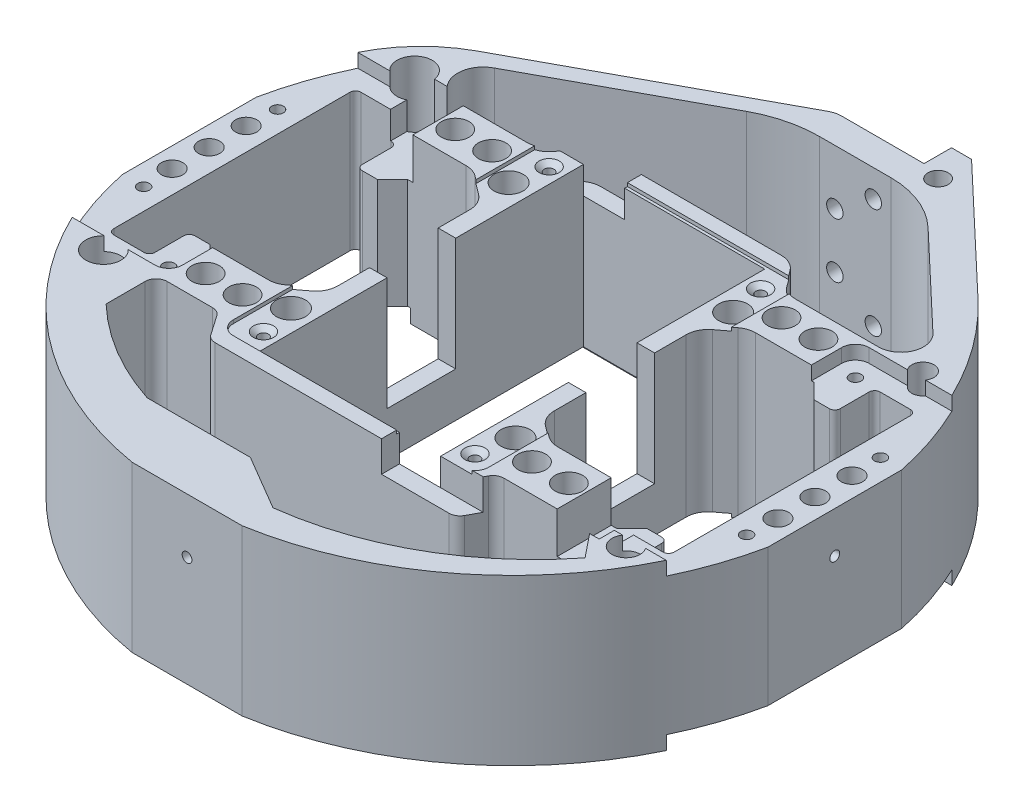
SolidWorks part; units mm, degrees
material "6061 Alloy"
ref_plane "Front Plane" through (0, 0, 0) normal (0, 0, 1) x (1, 0, 0)
ref_plane "Top Plane" through (0, 0, 0) normal (0, 1, 0) x (1, 0, 0)
ref_plane "Right Plane" through (0, 0, 0) normal (1, 0, 0) x (0, 0, -1)
sketch "Sketch1" plane through (0, 0, 0) normal (0, 1, 0) x (1, 0, 0)
  line L0 (-1000, 0) -> (49000, 0) construction
  line L1 (0, -1000) -> (0, 49000) construction
  line L2 (20.955, 37.465) -> (-20.955, 37.465)
  line L3 (-20.955, 37.465) -> (-20.955, 0)
  line L4 (-53.975, 19.3675) -> (-50.4825, 19.3675)
  line L5 (-50.4825, 19.3675) -> (-46.99, 22.86)
  line L6 (-46.99, 22.86) -> (-33.4518, 22.86)
  line L7 (-30.3916, 21.8348) -> (-27.0388, 19.3044)
  line L8 (-74.6125, 15.473) -> (-74.6125, -15.473)
  line L9 (-25.019, 15.2496) -> (-25.019, 0)
  line L10 (74.6125, 15.473) -> (74.6125, -15.473)
  line L11 (0, 76.2) -> (4.1152, 76.2) construction
  line L12 (-55.245, 20.6375) -> (-55.245, 27.305)
  line L13 (-56.515, 28.575) -> (-63.5, 28.575)
  line L14 (-64.77, 27.305) -> (-64.77, -27.305)
  line L15 (64.77, 27.305) -> (64.77, -27.305)
  line L16 (56.515, 28.575) -> (63.5, 28.575)
  line L17 (55.245, 20.6375) -> (55.245, 27.305)
  line L19 (0, 76.2) -> (19.05, 76.2)
  line L20 (25.019, 15.2496) -> (25.019, 0)
  line L21 (-20.846, 41.3381) -> (0, 41.3381)
  line L22 (30.3916, 21.8348) -> (27.0388, 19.3044)
  line L23 (46.99, 22.86) -> (33.4518, 22.86)
  line L24 (46.99, 22.86) -> (50.4825, 19.3675)
  line L25 (53.975, 19.3675) -> (50.4825, 19.3675)
  line L26 (20.955, 37.465) -> (20.955, 0)
  line L27 (20.955, -37.465) -> (20.955, 0)
  line L28 (53.975, -19.3675) -> (50.4825, -19.3675)
  line L29 (46.99, -22.86) -> (50.4825, -19.3675)
  line L30 (46.99, -22.86) -> (33.4518, -22.86)
  line L31 (30.3916, -21.8348) -> (27.0388, -19.3044)
  line L32 (24.9874, 39.2758) -> (27.197, 36.2837)
  line L33 (25.019, -15.2496) -> (25.019, 0)
  line L34 (19.05, 76.2) -> (19.05, 82.55)
  line L35 (19.05, 82.55) -> (23.6855, 82.55)
  line L36 (55.245, -20.6375) -> (55.245, -27.305)
  line L37 (56.515, -28.575) -> (63.5, -28.575)
  line L38 (-56.515, -28.575) -> (-63.5, -28.575)
  line L39 (-55.245, -20.6375) -> (-55.245, -27.305)
  line L40 (-23.8543, -60.4955) -> (0, -60.4955)
  line L41 (52.4298, 55.2951) -> (23.6855, 82.55)
  line L42 (-25.019, -15.2496) -> (-25.019, 0)
  line L43 (31.2835, 34.2214) -> (50.4563, 34.2214)
  line L44 (-30.3916, -21.8348) -> (-27.0388, -19.3044)
  line L45 (-46.99, -22.86) -> (-33.4518, -22.86)
  line L46 (-50.4825, -19.3675) -> (-46.99, -22.86)
  line L47 (-53.975, -19.3675) -> (-50.4825, -19.3675)
  line L48 (-20.955, -37.465) -> (-20.955, 0)
  line L49 (20.955, -37.465) -> (-20.955, -37.465)
  line L50 (-44.8593, -34.8822) -> (-34.3568, -34.8822)
  line L51 (-47.0915, 34.5231) -> (-31.087, 34.5231)
  line L52 (-27.0577, 36.5094) -> (-24.8753, 39.3518)
  line L53 (0, 41.3381) -> (20.9009, 41.3381)
  line L54 (54.0568, 43.2516) -> (32.3487, 63.8349)
  line L55 (18.015, 69.55) -> (1.5516, 69.55)
  line L56 (-32.2697, -35.9746) -> (-29.1259, -40.5071)
  line L57 (-27.0388, -41.5995) -> (27.0388, -41.5995)
  line L58 (-47.3993, -37.4222) -> (-47.3993, -46.4548)
  line L59 (54.276, -36.2937) -> (58.8069, -41.9283)
  line L60 (31.2258, -36.6729) -> (29.2707, -40.272)
  line L61 (52.2966, -35.3453) -> (33.4578, -35.3453)
  line L62 (-11.9532, 66.1301) -> (-49.7073, 45.6984)
  line L63 (-55.1504, 47.0849) -> (-2.539, 75.557)
  line L64 (0, -60.4955) -> (12.7, -67.9689)
  line L65 (12.7, -75.1342) -> (-12.7, -75.1342)
  arc A0 (-55.1504, 47.0849) -> (-68.875, 32.5987) centre (-39.8854, 18.8779) ccw
  arc A1 (63.5, -28.575) -> (64.77, -27.305) centre (63.5, -27.305) ccw
  arc A2 (64.77, 27.305) -> (63.5, 28.575) centre (63.5, 27.305) ccw
  arc A3 (-63.5, -28.575) -> (-64.77, -27.305) centre (-63.5, -27.305) cw
  arc A4 (-63.5, 28.575) -> (-64.77, 27.305) centre (-63.5, 27.305) ccw
  arc A5 (74.6125, 15.473) -> (52.4298, 55.2951) centre (0, 0) ccw
  arc A6 (-74.6125, -15.473) -> (-12.7, -75.1342) centre (0, 0) ccw
  arc A7 (55.245, -27.305) -> (56.515, -28.575) centre (56.515, -27.305) ccw
  arc A8 (56.515, 28.575) -> (55.245, 27.305) centre (56.515, 27.305) ccw
  arc A9 (-56.515, -28.575) -> (-55.245, -27.305) centre (-56.515, -27.305) ccw
  arc A10 (-55.245, 27.305) -> (-56.515, 28.575) centre (-56.515, 27.305) ccw
  arc A15 (50.4563, 34.2214) -> (54.0568, 43.2516) centre (50.4563, 39.4543) ccw
  arc A16 (-49.7073, 45.6984) -> (-47.0915, 34.5231) centre (-47.0915, 40.4169) ccw
  arc A17 (32.3487, 63.8349) -> (18.015, 69.55) centre (18.015, 48.7178) ccw
  arc A18 (-68.875, 32.5987) -> (-74.6125, 15.473) centre (0, 0) ccw
  arc A19 (12.7, -67.9689) -> (58.8069, -41.9283) centre (4.0432, 1.1967) ccw
  arc A20 (-47.3993, -46.4548) -> (-23.8543, -60.4955) centre (-4.9282, -1.9967) ccw
  arc A21 (12.7, -75.1342) -> (74.6125, -15.473) centre (0, 0) ccw
  circle A22 centre (23.6855, 74.8125) radius 2.3565
  circle A23 centre (-25.954, 25.1591) radius 3.3565
  arc A24 (-30.3916, -21.8348) -> (-33.4518, -22.86) centre (-33.4518, -17.78) cw
  arc A25 (-33.4518, 22.86) -> (-30.3916, 21.8348) centre (-33.4518, 17.78) cw
  arc A26 (30.3916, 21.8348) -> (33.4518, 22.86) centre (33.4518, 17.78) cw
  arc A27 (33.4518, -22.86) -> (30.3916, -21.8348) centre (33.4518, -17.78) cw
  arc A28 (27.0388, -19.3044) -> (25.019, -15.2496) centre (30.099, -15.2496) cw
  arc A29 (25.019, 15.2496) -> (27.0388, 19.3044) centre (30.099, 15.2496) cw
  arc A30 (-25.019, -15.2496) -> (-27.0388, -19.3044) centre (-30.099, -15.2496) cw
  arc A31 (-27.0388, 19.3044) -> (-25.019, 15.2496) centre (-30.099, 15.2496) cw
  arc A32 (53.975, -19.3675) -> (55.245, -20.6375) centre (53.975, -20.6375) cw
  arc A34 (55.245, 20.6375) -> (53.975, 19.3675) centre (53.975, 20.6375) cw
  arc A37 (-55.245, -20.6375) -> (-53.975, -19.3675) centre (-53.975, -20.6375) cw
  arc A38 (-53.975, 19.3675) -> (-55.245, 20.6375) centre (-53.975, 20.6375) cw
  circle A40 centre (-41.9877, 28.8501) radius 3.175
  circle A41 centre (41.9877, 28.8501) radius 3.175
  circle A42 centre (-41.9877, -28.8501) radius 3.175
  circle A43 centre (41.9877, -28.8501) radius 3.175
  circle A44 centre (-33.4518, 28.8501) radius 3.175
  circle A45 centre (33.4518, 28.8501) radius 3.175
  circle A46 centre (-33.4518, -28.8501) radius 3.175
  circle A47 centre (33.4518, -28.8501) radius 3.175
  circle A48 centre (-58.4996, 35.9746) radius 4.0647
  circle A49 centre (60.46, 34.5231) radius 2.5554
  circle A50 centre (-58.4996, -35.9746) radius 4.0647
  circle A51 centre (61.2367, -34.8822) radius 3.2423
  circle A52 centre (25.954, 25.1591) radius 3.3565
  circle A53 centre (25.954, -25.1591) radius 3.3565
  circle A54 centre (-25.954, -25.1591) radius 3.3565
  arc A55 (-27.0388, -41.5995) -> (-29.1259, -40.5071) centre (-27.0388, -39.0595) cw
  arc A56 (-34.3568, -34.8822) -> (-32.2697, -35.9746) centre (-34.3568, -37.4222) cw
  circle A57 centre (70.0256, 8.5625) radius 2.4628
  circle A58 centre (-70.0256, 8.5625) radius 2.4628
  circle A59 centre (70.0256, -8.5625) radius 2.4628
  circle A60 centre (-70.0256, -8.5625) radius 2.4628
  arc A61 (54.276, -36.2937) -> (52.2966, -35.3453) centre (52.2966, -37.8853) ccw
  arc A62 (31.2258, -36.6729) -> (33.4578, -35.3453) centre (33.4578, -37.8853) cw
  arc A63 (29.2707, -40.272) -> (27.0388, -41.5995) centre (27.0388, -39.0595) cw
  arc A64 (-44.8593, -34.8822) -> (-47.3993, -37.4222) centre (-44.8593, -37.4222) ccw
  circle A69 centre (-70.0256, 0) radius 2.4628
  circle A70 centre (70.0256, 0) radius 2.4628
  arc A71 (27.197, 36.2837) -> (31.2835, 34.2214) centre (31.2835, 39.3014) ccw
  arc A72 (20.9009, 41.3381) -> (24.9874, 39.2758) centre (20.9009, 36.2581) cw
  arc A73 (-31.087, 34.5231) -> (-27.0577, 36.5094) centre (-31.087, 39.6031) ccw
  arc A74 (-24.8753, 39.3518) -> (-20.846, 41.3381) centre (-20.846, 36.2581) cw
  arc A75 (-11.9532, 66.1301) -> (1.5516, 69.55) centre (1.5516, 41.1755) cw
  arc A76 (-2.539, 75.557) -> (0, 76.2) centre (0, 70.8654) cw
  point P34 (0, 37.465)
  point P44 (64.77, -28.575)
  point P49 (64.77, 0)
  point P50 (-64.77, 0)
  point P52 (55.245, -28.575)
  point P62 (64.77, 28.575)
  point P65 (-64.77, -28.575)
  point P68 (-64.77, 28.575)
  point P70 (-74.6125, 0)
  point P96 (-31.75, -22.86)
  point P99 (55.245, 28.575)
  point P103 (-55.245, -28.575)
  point P106 (-55.245, 28.575)
  point P111 (-48.26, -22.86)
  point P114 (48.26, -22.86)
  point P117 (48.26, 22.86)
  point P120 (-48.26, 22.86)
  point P124 (-31.75, 22.86)
  point P127 (31.75, 22.86)
  point P130 (31.75, -22.86)
  point P133 (25.019, -17.78)
  point P136 (25.019, 17.78)
  point P139 (-25.019, -17.78)
  point P142 (-25.019, 17.78)
  point P145 (55.245, -19.3675)
  point P148 (48.26, -19.3675)
  point P151 (55.245, 19.3675)
  point P154 (48.26, 19.3675)
  point P157 (-48.26, -19.3675)
  point P160 (-55.245, -19.3675)
  point P163 (-55.245, 19.3675)
  point P166 (-48.26, 19.3675)
  point P195 (0, -41.5995)
  point P218 (53.5134, -35.3453)
  point P221 (31.947, -35.3453)
  point P224 (28.5496, -41.5995)
  point P258 (-5.6338, 69.55)
  dimension "D2" = 41.91
  dimension "D7" = 1.27
  dimension "D10" = 1.27
  dimension "D16" = 21.971
  dimension "D3" = 5.08
  dimension "D22" = 1.27
  dimension "D23" = 2.54
  dimension "D14" = 6.35
  dimension "D24" = 38.735
  dimension "D25" = 5.08
  dimension "D26" = 4.6355
  dimension "D27" = 21.971
  dimension "D19" = 2.54
  dimension "D33" = 45
  dimension "D4" = 16.51
  dimension "D5" = 45.72
  dimension "D6" = 74.93
  dimension "D8" = 149.225
  dimension "D9" = 9.525
  dimension "D11" = 45
  dimension "D12" = 4.064
  dimension "D13" = 57.15
  dimension "D15" = 35.56
  dimension "D18" = 19.05
  dimension "D20" = 7.62
  dimension "D21" = 25.4
  dimension "D28" = 76.2
  dimension "D29" = 3.81
  dimension "D31" = 45
  dimension "D32" = 21.971
  dimension "D34" = 21.971
  dimension "D35" = 45
extrude "Boss-Extrude1" add sketch "Sketch1" along normal blind 38.1
ref_plane "Plane1" through (0, 19.05, 0) normal (0, 1, 0) x (-1, 0, 0)
ref_plane "Plane2" through (0, 0, 0) normal (-1, 0, 0) x (0, 0, 1)
sketch "Sketch2" plane through (0, 38.1, 0) normal (0, 1, 0) x (1, 0, 0)
  line L0 (-25.019, -15.2496) -> (-25.019, 15.2496) construction
  line L1 (-25.019, 7.9375) -> (-20.955, 7.9375)
  line L2 (-25.019, 7.9375) -> (-25.019, -7.9375)
  line L3 (-25.019, -7.9375) -> (-20.955, -7.9375)
  line L4 (-20.955, 7.9375) -> (-20.955, -7.9375)
  line L5 (-20.955, 37.465) -> (-20.955, -37.465) construction
  line L6 (20.955, -37.465) -> (20.955, 37.465) construction
  line L7 (20.955, 7.9375) -> (25.019, 7.9375)
  line L8 (20.955, 7.9375) -> (20.955, -7.9375)
  line L9 (20.955, -7.9375) -> (25.019, -7.9375)
  line L10 (25.019, 7.9375) -> (25.019, -7.9375)
  line L11 (25.019, 15.2496) -> (25.019, -15.2496) construction
  line L12 (25.019, 0) -> (-25.019, 0) construction
  dimension "D1" = 15.875
extrude "Cut-Extrude1" cut sketch "Sketch2" against normal blind 26.9875
sketch "Sketch3" plane through (0, 38.1, 0) normal (0, 1, 0) x (1, 0, 0)
  line L1 (-49.53, 33.02) -> (-80.0114, 33.02)
  line L2 (-46.355, 29.845) -> (-46.355, -29.845)
  line L3 (-49.53, -33.02) -> (-80.0114, -33.02)
  line L4 (-80.0114, 33.02) -> (-80.0114, -33.02)
  line L6 (-55.245, 20.6375) -> (-55.245, 27.305) construction
  line L7 (0, -1000) -> (0, 49000) construction
  line L8 (80.0114, 33.02) -> (80.0114, -33.02)
  line L9 (49.53, -33.02) -> (80.0114, -33.02)
  line L10 (46.355, 29.845) -> (46.355, -29.845)
  line L11 (49.53, 33.02) -> (80.0114, 33.02)
  arc A0 (-46.355, -29.845) -> (-49.53, -33.02) centre (-49.53, -29.845) cw
  arc A1 (-49.53, 33.02) -> (-46.355, 29.845) centre (-49.53, 29.845) cw
  arc A2 (49.53, 33.02) -> (46.355, 29.845) centre (49.53, 29.845) ccw
  arc A3 (46.355, -29.845) -> (49.53, -33.02) centre (49.53, -29.845) ccw
  dimension "D2" = 3.175
  dimension "D1" = 8.89
  dimension "D3" = 66.04
  dimension "D4" = 33.02
extrude "Cut-Extrude2" cut sketch "Sketch3" against normal blind 3.175
sketch "Sketch4" plane through (0, 34.925, 0) normal (0, 1, 0) x (1, 0, 0)
  line L2 (-1000, 0) -> (49000, 0) construction
  line L3 (0, -1000) -> (0, 49000) construction
  circle A0 centre (-50.8, 28.575) radius 1.3525
  circle A1 centre (-69.6913, 15.473) radius 1.3525
  circle A2 centre (69.6912, 15.473) radius 1.3526
  circle A3 centre (50.8, 28.575) radius 1.3525
  circle A4 centre (50.8, -28.575) radius 1.3525
  circle A5 centre (69.6912, -15.473) radius 1.3526
  circle A6 centre (-69.6913, -15.473) radius 1.3525
  circle A7 centre (-50.8, -28.575) radius 1.3525
  dimension "D1" = 2.7051
  dimension "D3" = 28.575
  dimension "D4" = 50.8
extrude "Cut-Extrude3" cut sketch "Sketch4" against normal blind 6.35
mirror "Mirror1" about plane through (0, 19.05, 0) normal (0, 1, 0) of "Cut-Extrude3", "Cut-Extrude2"
sketch "Sketch5" plane through (0, 34.925, 0) normal (0, 1, 0) x (1, 0, 0)
  line L1 (-45.7864, 36.5249) -> (-56.6704, 36.5249)
  line L2 (-56.6704, 36.5249) -> (-56.6704, 17.5524)
  line L3 (-56.6704, 17.5524) -> (-45.7864, 17.5524)
  line L4 (-45.7864, 36.5249) -> (-45.7864, 17.5524)
  line L5 (45.7864, -36.5249) -> (56.6704, -36.5249)
  line L6 (56.6704, -36.5249) -> (56.6704, -17.5524)
  line L7 (56.6704, -17.5524) -> (45.7864, -17.5524)
  line L8 (45.7864, -36.5249) -> (45.7864, -17.5524)
  line L10 (-57.3818, 22.86) -> (-41.566, 22.86) [skipped]
  line L11 (57.3818, -22.86) -> (41.566, -22.86) [skipped]
  dimension "D1" = 2
extrude "Cut-Extrude4" cut sketch "Sketch5" against normal mid plane 12.7
sketch "Sketch9" plane through (0, 38.1, 0) normal (0, 1, 0) x (1, 0, 0)
  line L0 (-20.955, 37.465) -> (-20.955, 7.9375) construction
  line L1 (-20.955, 34.3266) -> (-11.43, 34.3266)
  line L2 (-20.955, 34.3266) -> (-20.955, 37.465)
  line L3 (-20.955, 45.3771) -> (-11.43, 45.3771)
  line L4 (-11.43, 34.3266) -> (-11.43, 45.3771)
  line L5 (20.955, -34.3266) -> (11.43, -34.3266)
  line L6 (20.955, -34.3266) -> (20.955, -37.465)
  line L7 (20.955, -45.3771) -> (11.43, -45.3771)
  line L8 (11.43, -34.3266) -> (11.43, -45.3771)
  line L9 (-20.955, 45.3771) -> (-29.4619, 45.3771)
  line L10 (-29.4619, 45.3771) -> (-29.4619, 37.465)
  line L11 (-29.4619, 37.465) -> (-20.955, 37.465)
  line L12 (20.955, -37.465) -> (32.398, -37.465)
  line L13 (32.398, -37.465) -> (32.398, -45.3771)
  line L14 (32.398, -45.3771) -> (20.955, -45.3771)
  dimension "D1" = 9.525
  dimension "D2" = 2
extrude "Cut-Extrude7" cut sketch "Sketch9" against normal blind 7.112
sketch "Sketch10" plane through (0, 0, -76.2) normal (0, 0, -1) x (-1, 0, 0)
  circle A0 centre (-13.97, 31.75) radius 1.8987
  circle A1 centre (-5.08, 25.4) radius 1.8986
  circle A2 centre (-5.08, 12.7) radius 1.8986
  circle A3 centre (-13.97, 6.35) radius 1.8987
  circle A4 centre (-13.97, 31.75) radius 1.8987 construction
  circle A5 centre (-5.08, 25.4) radius 1.8986 construction
  circle A6 centre (-5.08, 12.7) radius 1.8986 construction
  circle A7 centre (-13.97, 6.35) radius 1.8987 construction
extrude "Cut-Extrude8" cut sketch "Sketch10" against normal up to next
sketch "Sketch11" plane through (-74.6125, 0, 0) normal (-1, 0, 0) x (0, 0, 1)
  line L0 (15.473, 34.925) -> (-15.473, 34.925) construction
  circle A0 centre (0, 25.4) radius 1.1303
  point P4 (0, 34.925)
  point P5 (0, 34.925)
  dimension "D1" = 2.2606
  dimension "D2" = 9.525
extrude "Cut-Extrude9" cut sketch "Sketch11" against normal blind 9.525
mirror "Mirror10" about plane through (0, 0, 0) normal (-1, 0, 0) of "Cut-Extrude9"
sketch "Sketch12" plane through (0, 0, 75.1342) normal (0, 0, 1) x (1, 0, 0)
  line L0 (-12.7, 38.1) -> (12.7, 38.1) construction
  circle A0 centre (0, 25.4) radius 1.1303
  point P4 (0, 38.1)
  dimension "D1" = 2.2606
  dimension "D2" = 12.7
extrude "Cut-Extrude10" cut sketch "Sketch12" against normal blind 9.525
sketch "Sketch13" plane through (0, 38.1, 0) normal (0, 1, 0) x (1, 0, 0)
  line L0 (-29.5275, -34.925) -> (-29.5275, -27.7953) construction
  line L1 (-26.3525, -38.1) -> (26.3525, -38.1)
  line L2 (-29.5275, -34.925) -> (-29.5275, 34.925)
  line L3 (-26.3525, 38.1) -> (26.3525, 38.1)
  line L4 (29.5275, -34.925) -> (29.5275, 34.925)
  line L5 (-29.5275, -38.1) -> (29.5275, 38.1) construction
  line L6 (-29.5275, 38.1) -> (29.5275, -38.1) construction
  line L7 (-21.9075, 38.1) -> (21.9075, 38.1) construction
  arc A0 (-29.5275, 34.925) -> (-26.3525, 38.1) centre (-26.3525, 34.925) cw
  arc A1 (26.3525, 38.1) -> (29.5275, 34.925) centre (26.3525, 34.925) cw
  arc A2 (26.3525, -38.1) -> (29.5275, -34.925) centre (26.3525, -34.925) ccw
  arc A3 (-26.3525, -38.1) -> (-29.5275, -34.925) centre (-26.3525, -34.925) cw
  point P0 (0, 0)
  dimension "D1" = 3.175
extrude "Cut-Extrude11" cut sketch "Sketch13" against normal blind 0.7937
mirror "Mirror11" about plane through (0, 19.05, 0) normal (0, 1, 0) of "Cut-Extrude11"
sketch "Sketch6" plane through (0, 0, 0) normal (0, -1, 0) x (1, 0, 0)
  line L0 (-1000, 0) -> (49000, 0) construction
  line L1 (0, -1000) -> (0, 49000) construction
  circle A0 centre (-24.4475, 33.02) radius 1.1303
  circle A1 centre (24.4475, 33.02) radius 1.1303
  circle A2 centre (24.4475, -33.02) radius 1.1303
  circle A3 centre (-24.4475, -33.02) radius 1.1303
  dimension "D1" = 33.02
  dimension "D2" = 24.4475
extrude "Cut-Extrude5" cut sketch "Sketch6" against normal blind 12.7
mirror "Mirror9" about plane through (0, 19.05, 0) normal (0, 1, 0) of "Cut-Extrude5"
chamfer "Chamfer1" distance 1.1951 angle 41 4 edges at (24.4475, 0.7937, 34.1503) (-24.4475, 0.7937, 34.1503) (-24.4475, 0.7937, -31.8897) (24.4475, 0.7937, -31.8897)
chamfer "Chamfer2" distance 1.1951 angle 41 4 edges at (-24.4475, 37.3062, 31.8897) (24.4475, 37.3062, 31.8897) (24.4475, 37.3062, -34.1503) (-24.4475, 37.3062, -34.1503)
